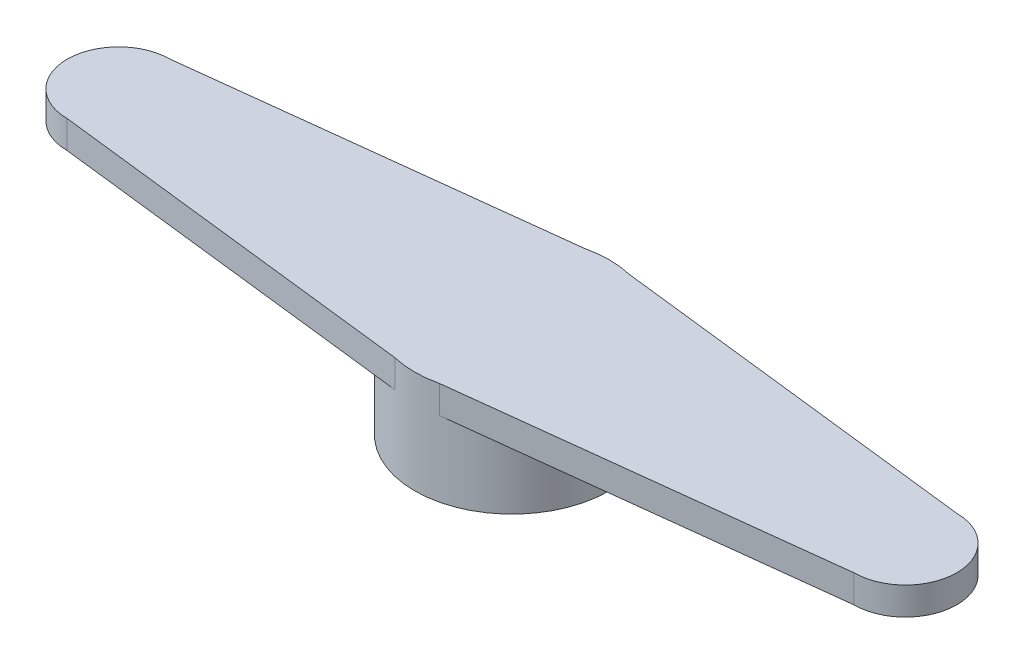
SolidWorks part; units mm, degrees
ref_plane "Alzado" through (0, 0, 0) normal (0, 0, 1) x (1, 0, 0)
ref_plane "Planta" through (0, 0, 0) normal (0, 1, 0) x (1, 0, 0)
ref_plane "Vista lateral" through (0, 0, 0) normal (1, 0, 0) x (0, 0, -1)
sketch "Croquis1" plane through (0, 0, 0) normal (0, 1, 0) x (1, 0, 0)
  circle A0 centre (0, 0) radius 2.5
  circle A1 centre (0, 0) radius 3.5
  dimension "D1" = 1
  dimension "D2" = 5
extrude "Saliente-Extruir1" add sketch "Croquis1" along normal blind 3.7
sketch "Croquis2" plane through (0, 3.7, 0) normal (0, 1, 0) x (1, 0, 0)
  line L0 (-16, 0) -> (16, 0) construction
  line L3 (-14.15, 1.85) -> (0, 3.5)
  line L4 (0, 3.5) -> (14.15, 1.85)
  line L5 (14.15, -1.85) -> (0, -3.5)
  line L6 (0, -3.5) -> (-14.15, -1.85)
  arc A0 (-14.15, 1.85) -> (-14.15, -1.85) centre (-14.15, 0) ccw
  arc A1 (14.15, -1.85) -> (14.15, 1.85) centre (14.15, 0) ccw
  circle A2 centre (0, 0) radius 3.5 construction
  point P6 (0, 0)
  dimension "D1" = 32
  dimension "D2" = 1.85
  dimension "D3" = 1.85
  dimension "D4" = 166.698
extrude "Saliente-Extruir2" add sketch "Croquis2" against normal blind 1
